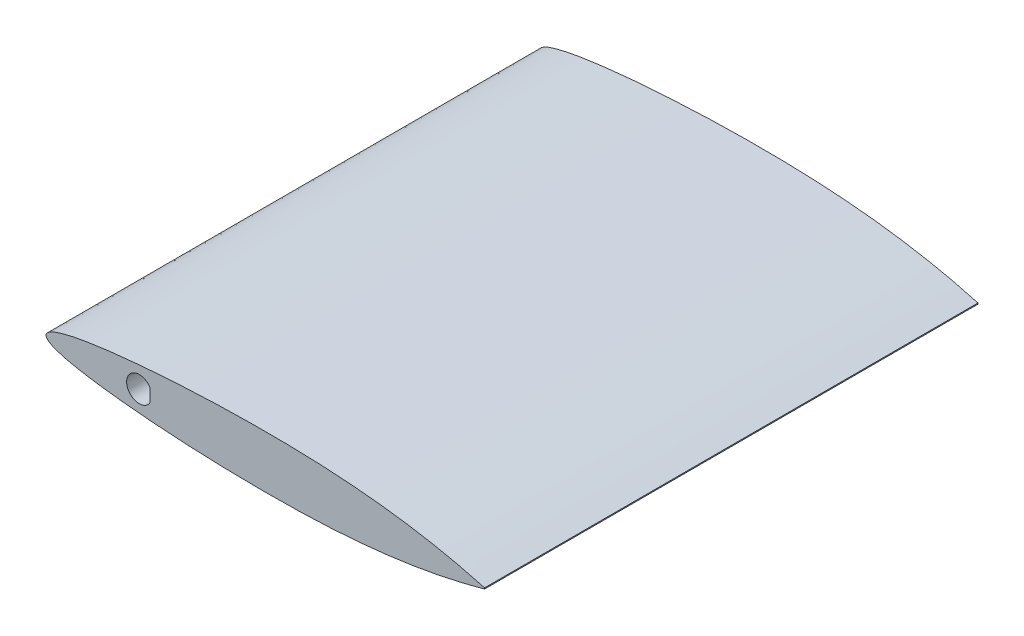
SolidWorks part; units mm, degrees
material "Maple"
ref_plane "Front Plane" through (0, 0, 0) normal (0, 0, 1) x (1, 0, 0)
ref_plane "Top Plane" through (0, 0, 0) normal (0, 1, 0) x (1, 0, 0)
ref_plane "Right Plane" through (0, 0, 0) normal (1, 0, 0) x (0, 0, -1)
curve "Curve3"
  spline degree 3 poles (101.6, 0.1219, 0) (99.9099, 0.5738, 0) (96.5445, 1.4735, 0) (89.7838, 2.9471, 0) (81.3219, 4.3668, 0) (71.1403, 5.4364, 0) (60.9671, 5.9966, 0) (50.8, 6.1452, 0) (40.6357, 5.9983, 0) (30.4708, 5.553, 0) (22.003, 4.9329, 0) (15.2308, 4.2232, 0) (10.9987, 3.6642, 0) (7.608, 3.0922, 0) (5.0721, 2.5808, 0) (2.8944, 1.9709, 0) (1.1817, 1.3642, 0) (-0.6746, 0, 0) (1.1817, -1.3642, 0) (2.8944, -1.9709, 0) (5.0721, -2.5808, 0) (7.608, -3.0922, 0) (10.9987, -3.6642, 0) (15.2308, -4.2232, 0) (22.003, -4.9329, 0) (30.4708, -5.553, 0) (40.6357, -5.9983, 0) (50.8, -6.1452, 0) (60.9671, -5.9966, 0) (71.1403, -5.4364, 0) (81.3219, -4.3668, 0) (89.7838, -2.9471, 0) (96.5445, -1.4735, 0) (99.9099, -0.5738, 0) (101.6, -0.1219, 0) knots 0 0 0 0 0.025456 0.050691 0.100669 0.150236 0.199601 0.248894 0.298185 0.347518 0.396944 0.421725 0.446593 0.459091 0.47168 0.48448 0.49114 0.5 0.50886 0.51552 0.52832 0.540909 0.553407 0.578275 0.603056 0.652482 0.701815 0.751106 0.800399 0.849764 0.899331 0.949309 0.974544 1 1 1 1
sketch "Sketch1" plane through (0, 0, 0) normal (0, 0, 1) x (1, 0, 0)
  line L0 (101.6, 0.1219) -> (101.6, -0.1219)
  spline S0 degree 3 poles (2808.3329, 9617.4645) (272.8572, -211.1663) (203.3622, -21.8091) (89.7838, 2.9471) (81.3219, 4.3668) (71.1403, 5.4364) (60.9671, 5.9966) (50.8, 6.1452) (40.6357, 5.9983) (30.4708, 5.553) (22.003, 4.9329) (15.2308, 4.2232) (10.9987, 3.6642) (7.608, 3.0922) (5.0721, 2.5808) (2.8944, 1.9709) (1.1817, 1.3642) (-0.6746, 0) (1.1817, -1.3642) (2.8944, -1.9709) (5.0721, -2.5808) (7.608, -3.0922) (10.9987, -3.6642) (15.2308, -4.2232) (22.003, -4.9329) (30.4708, -5.553) (40.6357, -5.9983) (50.8, -6.1452) (60.9671, -5.9966) (71.1403, -5.4364) (81.3219, -4.3668) (89.7838, -2.9471) (203.3598, 21.8086) (272.8542, 211.1583) (2808.1686, -9616.8277) knots -1.590548 -1.590548 -1.590548 -1.590548 0.025456 0.050691 0.100669 0.150236 0.199601 0.248894 0.298185 0.347518 0.396944 0.421725 0.446593 0.459091 0.47168 0.48448 0.49114 0.5 0.50886 0.51552 0.52832 0.540909 0.553407 0.578275 0.603056 0.652482 0.701815 0.751106 0.800399 0.849764 0.899331 0.949309 0.974544 2.590514 2.590514 2.590514 2.590514 only from (101.6, 0.1219) to (101.6, -0.1219) construction
  spline S1 degree 3 poles (101.6, 0.1219) (99.9099, 0.5738) (96.5445, 1.4735) (89.7838, 2.9471) (81.3219, 4.3668) (71.1403, 5.4364) (60.9671, 5.9966) (50.8, 6.1452) (40.6357, 5.9983) (30.4708, 5.553) (22.003, 4.9329) (15.2308, 4.2232) (10.9987, 3.6642) (7.608, 3.0922) (5.0721, 2.5808) (2.8944, 1.9709) (1.1817, 1.3642) (-0.6746, 0) (1.1817, -1.3642) (2.8944, -1.9709) (5.0721, -2.5808) (7.608, -3.0922) (10.9987, -3.6642) (15.2308, -4.2232) (22.003, -4.9329) (30.4708, -5.553) (40.6357, -5.9983) (50.8, -6.1452) (60.9671, -5.9966) (71.1403, -5.4364) (81.3219, -4.3668) (89.7838, -2.9471) (96.5445, -1.4735) (99.9099, -0.5738) (101.6, -0.1219) knots 0 0 0 0 0.025456 0.050691 0.100669 0.150236 0.199601 0.248894 0.298185 0.347518 0.396944 0.421725 0.446593 0.459091 0.47168 0.48448 0.49114 0.5 0.50886 0.51552 0.52832 0.540909 0.553407 0.578275 0.603056 0.652482 0.701815 0.751106 0.800399 0.849764 0.899331 0.949309 0.974544 1 1 1 1
extrude "Boss-Extrude1" add sketch "Sketch1" along normal blind 114.3
sketch "Sketch2" plane through (0, 0, 114.3) normal (0, 0, 1) x (1, 0, 0)
  line L1 (101.6, 0.1219) -> (101.6, -0.1219)
  line L4 (24.0567, 1.5875) -> (24.0567, -1.5875)
  arc A0 (24.0567, 1.5875) -> (24.0567, -1.5875) centre (21.6, 0) ccw
  dimension "D1" = 5.85
  dimension "D2" = 3.175
  dimension "D3" = 80
extrude "Cut-Extrude1" cut sketch "Sketch2" against normal through all contours L4 A0
